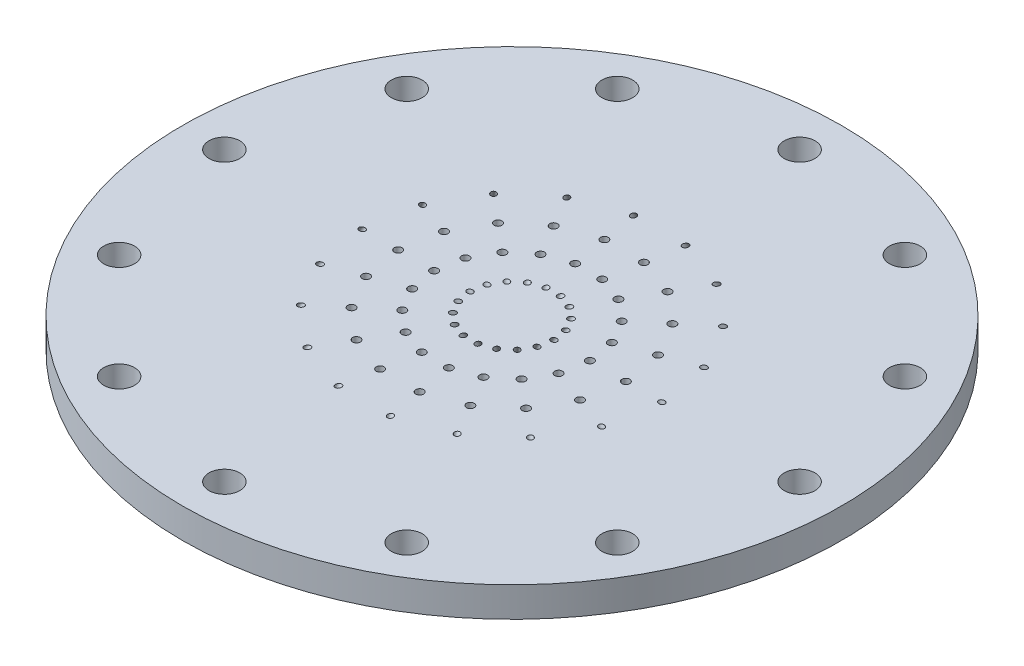
SolidWorks part; units mm, degrees
material "6061-T6 (SS)"
ref_plane "Front Plane" through (0, 0, 0) normal (0, 0, 1) x (1, 0, 0)
ref_plane "Top Plane" through (0, 0, 0) normal (0, 1, 0) x (1, 0, 0)
ref_plane "Right Plane" through (0, 0, 0) normal (1, 0, 0) x (0, 0, -1)
sketch "Sketch1" plane through (0, 0, 0) normal (0, 1, 0) x (1, 0, 0)
  circle A0 centre (0, 0) radius 69.85
  dimension "D1" = 139.7
extrude "Boss-Extrude1" add sketch "Sketch1" along normal blind 6.35 contours A0
sketch "Sketch2" plane through (0, 6.35, 0) normal (0, 1, 0) x (1, 0, 0)
  circle A0 centre (0, 0) radius 8.89
  circle A1 centre (0, 0) radius 16.51
  circle A2 centre (0, 0) radius 24.13
  circle A3 centre (0, 0) radius 31.75
  dimension "D1" = 17.78
  dimension "D2" = 33.02
  dimension "D3" = 48.26
  dimension "D4" = 63.5
sketch "Sketch3" plane through (0, 0, 0) normal (0, 0, 1) x (1, 0, 0)
  line L0 (8.89, 6.35) -> (0, -9.0479)
  line L1 (8.89, 6.35) -> (-8.89, 6.35) construction
  line L2 (16.51, 6.35) -> (-16.51, 6.35) construction
  line L3 (0, 0) -> (0, -9.0479) construction
  line L4 (0, -9.0479) -> (-8.5376, -4.1187) construction
  dimension "D1" = 30
ref_plane "Plane1" through (-3.9179, -6.7859, 0) normal (0.5, 0.866, 0) x (-0.866, 0.5, 0)
sketch "Sketch4" plane through (-3.9179, -6.7859, 0) normal (0.5, 0.866, 0) x (-0.866, 0.5, 0)
  line L0 (-4.524, 0) -> (5.3344, 0) construction
  circle A0 centre (-4.524, 0) radius 0.5906
  dimension "D1" = 1.1811
extrude "Cut-Extrude1" cut sketch "Sketch4" along normal through all
sketch "Sketch5" plane through (0, 0, 0) normal (0, 0, 1) x (1, 0, 0)
  line L0 (31.75, 6.35) -> (35.4162, 0)
  line L3 (31.75, 6.35) -> (-31.75, 6.35) construction
  line L4 (35.4162, 0) -> (0, 0) construction
  line L5 (31.75, 6.35) -> (52.6029, 18.3894) construction
  dimension "D1" = 60
ref_plane "Plane2" through (5.1879, -8.9857, 0) normal (0.5, -0.866, 0) x (0.866, 0.5, 0)
sketch "Sketch6" plane through (5.1879, -8.9857, 0) normal (0.5, -0.866, 0) x (0.866, 0.5, 0)
  circle A0 centre (30.6713, 0) radius 0.5906
  dimension "D1" = 1.1811
extrude "Cut-Extrude2" cut sketch "Sketch6" against normal through all both and the other way through all
sketch "Sketch7" plane through (0, 6.35, 0) normal (0, 1, 0) x (1, 0, 0)
  line L0 (0, 0) -> (31.75, 0) construction
  circle A0 centre (0, 0) radius 31.75 construction
  circle A1 centre (24.13, 0) radius 0.8255
  circle A2 centre (0, 0) radius 24.13 construction
  circle A3 centre (16.51, 0) radius 0.8255
  circle A7 centre (0, 0) radius 16.51 construction
  dimension "D1" = 1.651
extrude "LOx Holes" cut sketch "Sketch7" against normal through all both and the other way through all
pattern_circular "CirPattern1" count 18 over 360 about axis through (0, 0, 0) along (0, 1, 0) of "Cut-Extrude1", "Cut-Extrude2", "LOx Holes"
sketch "Sketch8" plane through (0, 0, 0) normal (0, -1, 0) x (1, 0, 0)
  circle A0 centre (0, 0) radius 60.96 construction
  circle A1 centre (-60.96, 0) radius 3.2639
  dimension "D1" = 121.92
  dimension "D2" = 6.5278
extrude "Cut-Extrude4" cut sketch "Sketch8" against normal through all
pattern_circular "CirPattern2" count 12 over 360 about axis through (0, 0, 0) along (0, 1, 0) of "Cut-Extrude4"
